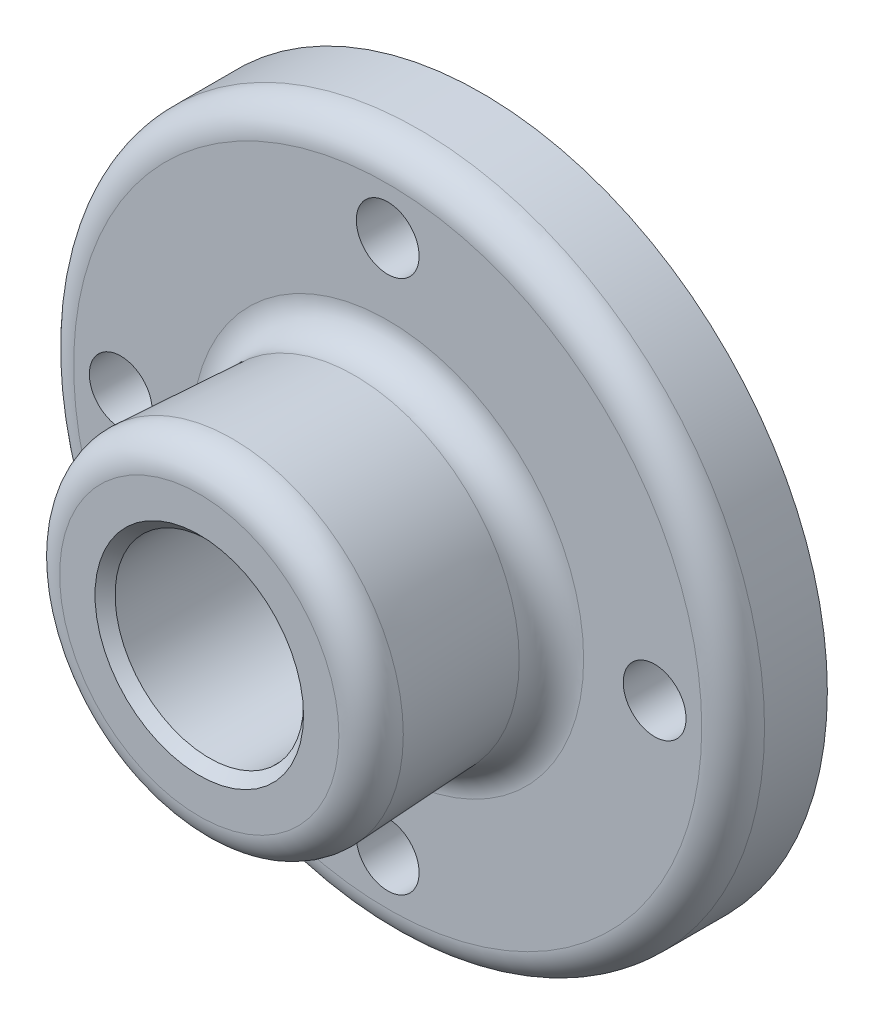
SolidWorks part; units mm, degrees
ref_plane "Front Plane" through (0, 0, 0) normal (0, 0, 1) x (1, 0, 0)
ref_plane "Top Plane" through (0, 0, 0) normal (0, 1, 0) x (1, 0, 0)
ref_plane "Right Plane" through (0, 0, 0) normal (1, 0, 0) x (0, 0, -1)
sketch "Sketch1" plane through (0, 0, 0) normal (0, 0, 1) x (1, 0, 0)
  circle A0 centre (0, 0) radius 69.85
  dimension "D1" = 139.7
extrude "Boss-Extrude1" add sketch "Sketch1" along normal blind 19.05
ref_plane "Plane1" through (0, 0, 57.15) normal (0, 0, 1) x (1, 0, 0)
sketch "Sketch2" plane through (0, 0, 19.05) normal (0, 0, 1) x (1, 0, 0)
  circle A0 centre (0, 0) radius 34.925
  dimension "D1" = 69.85
sketch "Sketch3" plane through (0, 0, 57.15) normal (0, 0, 1) x (1, 0, 0)
  circle A0 centre (0, 0) radius 34.925
  dimension "D1" = 69.85
extrude "Boss-Extrude2" add sketch "Sketch3" against normal up to next (38.1 mm away) draft 3
sketch "Sketch4" plane through (0, 0, 19.05) normal (0, 0, 1) x (1, 0, 0)
  circle A0 centre (0, 0) radius 19.05
  dimension "D1" = 38.1
extrude "Cut-Extrude1" cut sketch "Sketch4" against normal through all
sketch "Sketch5" plane through (0, 0, 57.15) normal (0, 0, 1) x (1, 0, 0)
  circle A0 centre (0, 0) radius 19.05
  dimension "D1" = 38.1
extrude "Bolt Hole" cut sketch "Sketch5" against normal through all
sketch "Sketch6" plane through (0, 0, 19.05) normal (0, 0, 1) x (1, 0, 0)
  circle A0 centre (0, 0) radius 53.975 construction
  circle A1 centre (0, 53.975) radius 6.35
  dimension "D1" = 107.95
  dimension "D2" = 12.7
extrude "Cut-Extrude3" cut sketch "Sketch6" against normal through all
pattern_circular "CirPattern2" count 4 over 360 about axis through (0, 0, 0) along (0, 0, 1) of "Cut-Extrude3"
fillet "Fillet1" radius 6.35 3 edges at (69.85, 0, 19.05) (32.9283, 0, 19.05) (34.925, 0, 57.15)
chamfer "Chamfer1" distance 2.032 angle 45 1 edges at (19.05, 0, 57.15)
